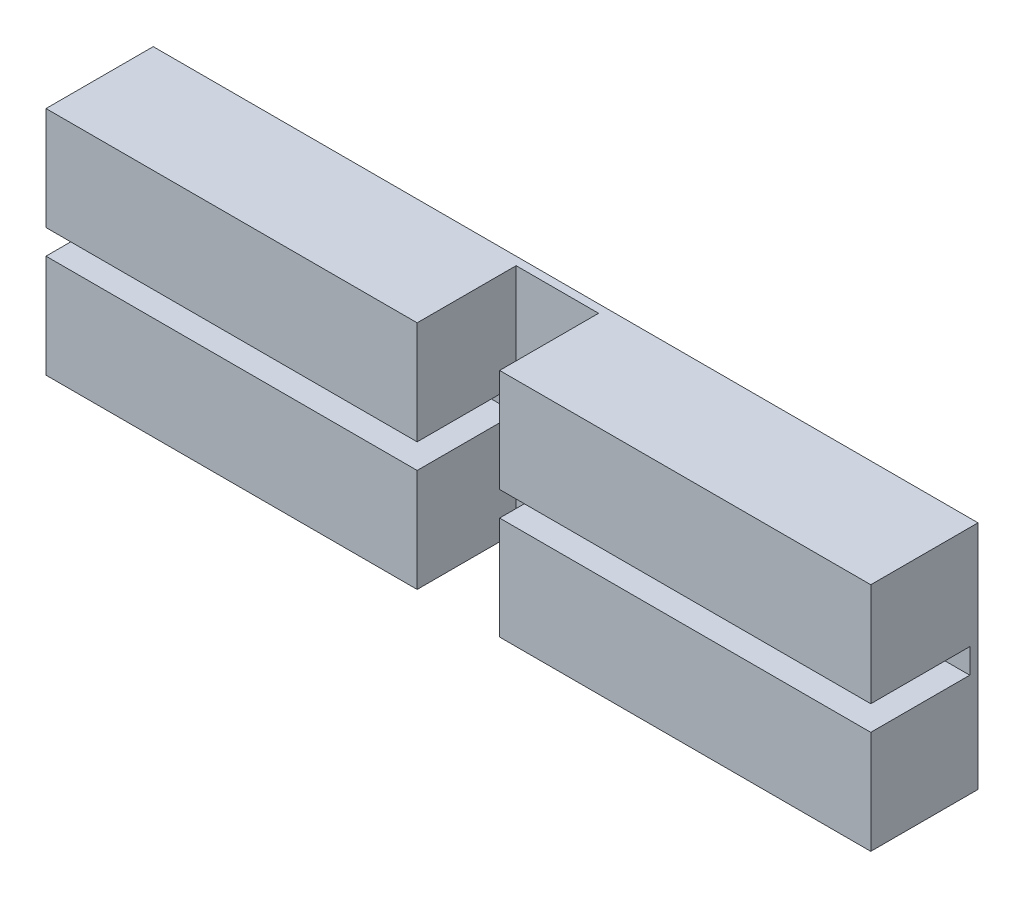
SolidWorks part; units mm, degrees
ref_plane "前视基准面" through (0, 0, 0) normal (0, 0, 1) x (1, 0, 0)
ref_plane "上视基准面" through (0, 0, 0) normal (0, 1, 0) x (1, 0, 0)
ref_plane "右视基准面" through (0, 0, 0) normal (1, 0, 0) x (0, 0, -1)
sketch "草图1" plane through (0, 0, 0) normal (0, 0, 1) x (1, 0, 0)
  line L1 (-10, -2.8) -> (10, -2.8)
  line L2 (-10, -2.8) -> (-10, 2.8)
  line L3 (-10, 2.8) -> (10, 2.8)
  line L4 (10, -2.8) -> (10, 2.8)
  line L5 (-10, -2.8) -> (10, 2.8) construction
  line L6 (-10, 2.8) -> (10, -2.8) construction
  point P0 (0, 0)
  dimension "D1" = 20
  dimension "D2" = 5.6
extrude "凸台-拉伸1" add sketch "草图1" along normal blind 2.6
sketch "草图2" plane through (10, 0, 0) normal (1, 0, 0) x (0, 0, -1)
  line L0 (-2.6, -2.8) -> (-2.6, 2.8) construction
  line L1 (-0.2, -0.3) -> (-2.6, -0.3)
  line L2 (-0.2, -0.3) -> (-0.2, 0.3)
  line L3 (-0.2, 0.3) -> (-2.6, 0.3)
  line L4 (-2.6, -0.3) -> (-2.6, 0.3)
  line L5 (0, -2.8) -> (0, 2.8) construction
  line L6 (-2.6, 2.8) -> (0, 2.8) construction
  line L7 (-2.6, -2.8) -> (0, -2.8) construction
  dimension "D1" = 0.2
  dimension "D2" = 2.5
  dimension "D3" = 2.5
extrude "切除-拉伸1" cut sketch "草图2" against normal through all
sketch "草图3" plane through (0, -2.8, 0) normal (0, -1, 0) x (1, 0, 0)
  line L0 (-10, 2.6) -> (10, 2.6) construction
  line L1 (1, 0.2) -> (-1, 0.2)
  line L2 (1, 0.2) -> (1, 2.6)
  line L3 (1, 2.6) -> (-1, 2.6)
  line L4 (-1, 0.2) -> (-1, 2.6)
  line L5 (-10, 0) -> (10, 0) construction
  line L6 (10, 2.6) -> (10, 0) construction
  line L7 (-10, 2.6) -> (-10, 0) construction
  point P8 (10, 1.3)
  dimension "D1" = 0.2
  dimension "D2" = 9
  dimension "D3" = 9
extrude "切除-拉伸2" cut sketch "草图3" against normal through all
